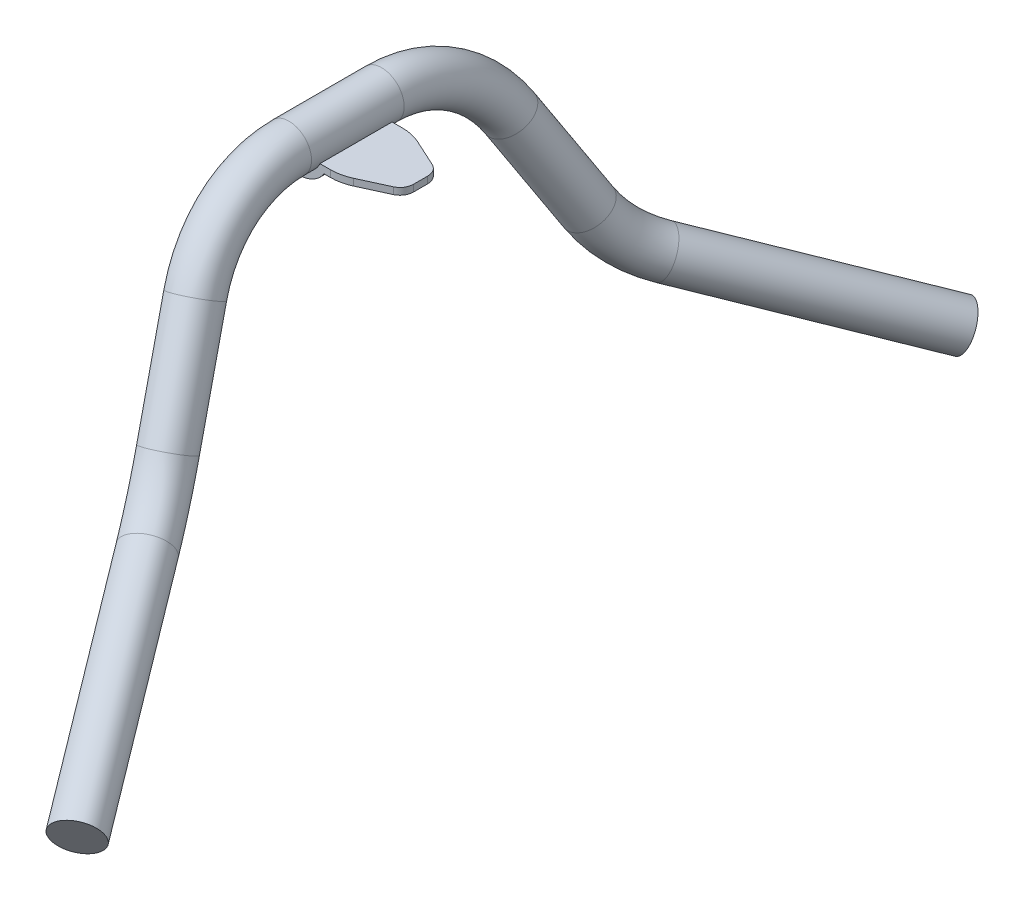
SolidWorks part; units mm, degrees
ref_plane "Front Plane" through (0, 0, 0) normal (0, 0, 1) x (1, 0, 0)
ref_plane "Top Plane" through (0, 0, 0) normal (0, 1, 0) x (1, 0, 0)
ref_plane "Right Plane" through (0, 0, 0) normal (1, 0, 0) x (0, 0, -1)
sketch "Sketch1" plane through (0, 0, 0) normal (0, 1, 0) x (1, 0, 0)
  line L0 (-34.798, 0) -> (33.8578, 0) construction
  line L1 (4.6071, 20.32) -> (-28.448, 20.32)
  line L2 (-34.798, 13.97) -> (-34.798, -13.97)
  line L3 (-28.448, -20.32) -> (4.6071, -20.32)
  line L4 (15.2063, -18.0028) -> (30.6118, -10.9289)
  line L5 (35.052, -4.004) -> (35.052, 4.004)
  line L6 (30.6118, 10.9289) -> (15.2063, 18.0028)
  arc A0 (-34.798, -13.97) -> (-28.448, -20.32) centre (-28.448, -13.97) ccw
  arc A1 (-28.448, 20.32) -> (-34.798, 13.97) centre (-28.448, 13.97) ccw
  arc A2 (4.6071, -20.32) -> (15.2063, -18.0028) centre (4.6071, 5.08) ccw
  arc A3 (4.6071, 20.32) -> (15.2063, 18.0028) centre (4.6071, -5.08) cw
  arc A4 (30.6118, -10.9289) -> (35.052, -4.004) centre (27.432, -4.004) ccw
  arc A5 (35.052, 4.004) -> (30.6118, 10.9289) centre (27.432, 4.004) ccw
  point P15 (-34.798, -20.32)
  point P18 (-34.798, 20.32)
  point P21 (10.16, -20.32)
  point P24 (10.16, 20.32)
  point P27 (35.052, -8.89)
  point P30 (35.052, 8.89)
  dimension "D6" = 6.35
  dimension "D7" = 25.4
  dimension "D8" = 7.62
  dimension "D1" = 69.85
  dimension "D2" = 40.64
  dimension "D3" = 17.78
  dimension "D4" = 44.958
  dimension "D5" = 34.798
extrude "Boss-Extrude1" add sketch "Sketch1" along normal mid plane 20.32
sketch "Sketch2" plane through (0, 0, 20.32) normal (0, 0, 1) x (1, 0, 0)
  line L0 (-34.798, 10.16) -> (-24.638, 10.16)
  line L1 (-28.448, 10.16) -> (4.6071, 10.16) construction
  line L2 (35.052, 10.16) -> (-1.3585, 10.16)
  line L3 (-34.798, 6.35) -> (-26.9104, 6.35)
  line L4 (35.052, 6.35) -> (0.9139, 6.35)
  line L5 (-34.798, 10.16) -> (-34.798, 6.35)
  line L6 (35.052, 10.16) -> (35.052, 6.35)
  arc A0 (-24.638, 10.16) -> (-1.3585, 10.16) centre (-12.9983, 15.24) ccw
  arc A1 (-26.9104, 6.35) -> (0.9139, 6.35) centre (-12.9983, 15.24) ccw
  dimension "D2" = 12.7
  dimension "D1" = 5.08
  dimension "D3" = 10.16
  dimension "D4" = 3.81
extrude "Cut-Extrude1" cut sketch "Sketch2" against normal through all flip side to cut
sketch "Sketch3" plane through (0, 0, 0) normal (0, 0, 1) x (1, 0, 0)
  circle A0 centre (-12.9983, 15.24) radius 12.7
  arc A1 (-24.638, 10.16) -> (-1.3585, 10.16) centre (-12.9983, 15.24) ccw construction
  dimension "D1" = 25.4
sketch3d "3DSketch1"
  line L0 (-12.9983, 15.24, 0) -> (-12.9983, 15.24, 26.0906)
  line L1 (-3.2257, -20.876, 88.7166) -> (11.2141, -74.2403, 118.47)
  line L2 (26.6346, -101.7196, 145.5709) -> (91.1417, -157.48, 249.5648)
  arc A0 (26.6346, -101.7196, 145.5709) -> (11.2141, -74.2403, 118.47) centre (47.9837, -37.3081, 166.8648) ccw
  arc A1 (-12.9983, 15.24, 26.0906) -> (-3.2257, -20.876, 88.7166) centre (5.5779, -53.4111, 26.0906) ccw
  point P3 (91.1417, -157.48, 249.5648)
  point P7 (16.2117, -92.71, 128.7678)
  point P9 (106.6222, -43.6032, 127.1162)
  point P11 (16.2117, -92.71, 128.7678)
  point P13 (-12.9983, 15.24, 68.58)
  point P14 (74.2291, -34.835, 26.0906)
  dimension "D8" = 71.12
  dimension "D1" = 68.58
  dimension "D2" = 29.21
  dimension "D3" = 107.95
  dimension "D4" = 127
  dimension "D5" = 104.14
  dimension "D6" = 172.72
  dimension "D7" = 156.21
sweep "Sweep1" add profiles "Sketch3" path "3DSketch1"
mirror "Mirror1" about plane through (0, 0, 0) normal (0, 0, 1) of bodies 103
